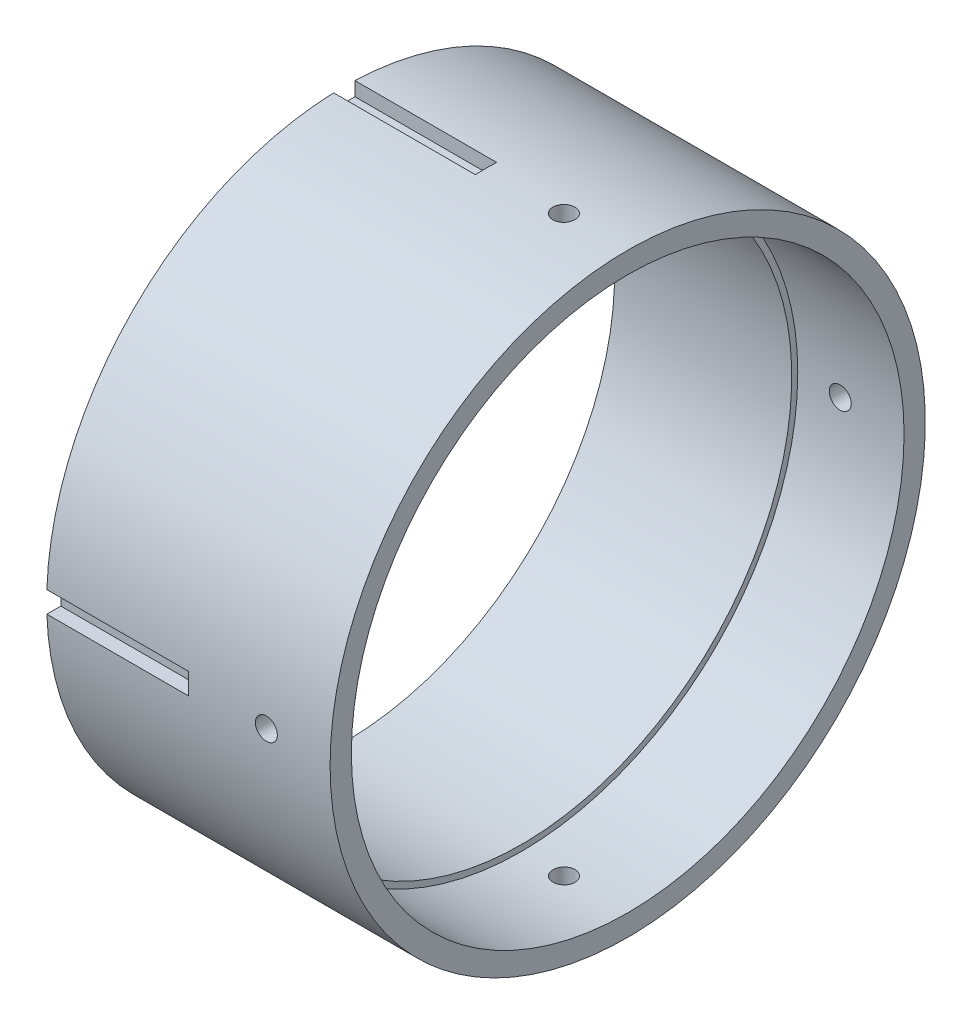
SolidWorks part; units mm, degrees
material "Alliage 1060"
ref_plane "Plan de face" through (0, 0, 0) normal (0, 0, 1) x (1, 0, 0)
ref_plane "Plan de dessus" through (0, 0, 0) normal (0, 1, 0) x (1, 0, 0)
ref_plane "Plan de droite" through (0, 0, 0) normal (1, 0, 0) x (0, 0, -1)
sketch "Esquisse1" plane through (0, 0, 0) normal (0, 0, 1) x (1, 0, 0)
  line L0 (0, 38.15) -> (25, 38.15)
  line L1 (25, 38.15) -> (25, 39)
  line L2 (25, 39) -> (40, 39)
  line L3 (40, 39) -> (40, 42)
  line L4 (40, 42) -> (0, 42)
  line L5 (0, 42) -> (0, 38.15)
  line L6 (0, 0) -> (35.5501, 0) construction
  dimension "D1" = 42
  dimension "D2" = 25
  dimension "D3" = 3
  dimension "D4" = 3.85
  dimension "D5" = 40
  dimension "D6" = 15
  dimension "D7" = 38.15
revolve "Révolution1" add sketch "Esquisse1" angle 360 about L6
hole_wizard "Dégagement M2.51" positions "Esquisse3D2" profile "Esquisse4" hole size "M2.5" standard "ISO" end condition through all
sketch3d "Esquisse3D2"
  line L2 (0, 0, 0) -> (0, 126.2496, 0) construction
  line L4 (0, 42, 0) -> (37.1483, 42, 0) construction
  point P0 (31, 42, 0)
  dimension "D1" = 31
sketch "Esquisse4" plane through (31, 42, 0) normal (1, 0, 0) x (0, 0, 1)
  line L0 (0, 0) -> (0, 84)
  line L1 (0, 84) -> (1.55, 84)
  line L2 (1.55, 84) -> (1.55, 0)
  line L5 (1.55, 0) -> (0, 0)
  line L11 (0, -6.35) -> (0, 107.95) construction
  dimension "Diamètre du perçage jusqu'au prochain" = 3.1
  dimension "Profondeur du perçage jusqu'au prochain" = 84
pattern_circular "Répétition circulaire1" count 2 every 90 about axis through (40, 0, 0) along (-1, 0, 0) of "Dégagement M2.51"
sketch "Esquisse5" plane through (0, 0, 0) normal (-1, 0, 0) x (0, 0, 1)
  line L0 (0, 0) -> (0, 80) construction
  line L1 (-1.5, 55) -> (1.5, 55)
  line L2 (-1.5, 55) -> (-1.5, 40)
  line L3 (-1.5, 40) -> (1.5, 40)
  line L4 (1.5, 55) -> (1.5, 40)
  point P7 (0, 40)
  dimension "D1" = 3
  dimension "D2" = 15
  dimension "D3" = 40
extrude "Enlèv. mat.-Extru.1" cut sketch "Esquisse5" against normal blind 20
pattern_circular "Répétition circulaire2" count 4 over 360 about axis through (0, 0, 0) along (1, 0, 0) of "Enlèv. mat.-Extru.1"
